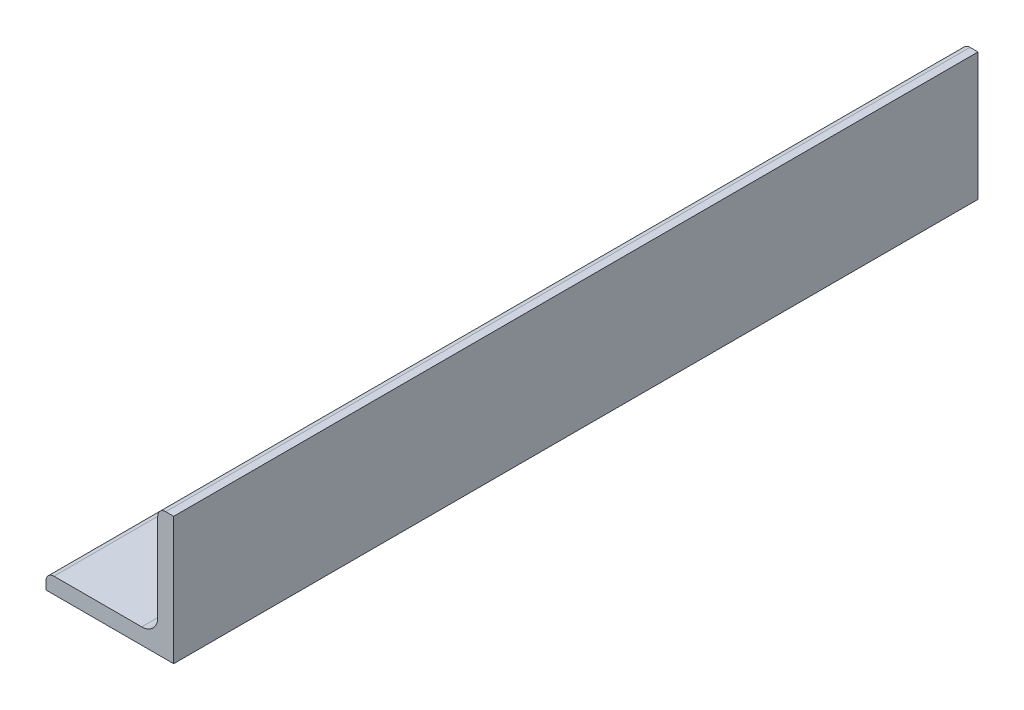
SolidWorks part; units mm, degrees
ref_plane "Front Plane" through (0, 0, 0) normal (0, 0, 1) x (1, 0, 0)
ref_plane "Top Plane" through (0, 0, 0) normal (0, 1, 0) x (1, 0, 0)
ref_plane "Right Plane" through (0, 0, 0) normal (1, 0, 0) x (0, 0, -1)
sketch "Sketch0" plane through (0, 0, 0) normal (0, 0, 1) x (1, 0, 0)
  line L0 (-12.7, -12.7) -> (12.7, -12.7)
  line L1 (12.7, -12.7) -> (12.7, 12.7)
  line L2 (12.7, 0) -> (0, 0) construction
  line L3 (0, 0) -> (0, -12.7) construction
  line L4 (9.525, -6.35) -> (9.525, 12.7) construction
  line L5 (6.35, -9.525) -> (-12.7, -9.525) construction
  arc A0 (9.525, -6.35) -> (6.35, -9.525) centre (6.35, -6.35) cw
  point P3 (8.5951, -8.5951)
  dimension "Inside Corner Radius" = 3.175
  dimension "Outside Height" = 25.4
  dimension "Inside Height" = 22.225
  dimension "Inside Width" = 22.225
  dimension "Wall Thickness" = 3.175
  dimension "D1" = 3.175
  dimension "Outside Width" = 25.4
sketch "Sketch1" plane through (0, 0, 0) normal (1, 0, 0) x (0, 0, -1)
  line L0 (609.6, 0) -> (-609.6, 0)
  point P4 (0, 0)
  dimension "Length" = 1219.2
sketch "Sketch2" plane through (0, 0, 0) normal (0, 0, 1) x (1, 0, 0)
  line L0 (-12.7, -12.7) -> (12.7, -12.7)
  line L1 (12.7, -12.7) -> (12.7, 12.7)
  line L2 (12.7, 12.7) -> (9.525, 12.7) construction
  line L3 (9.525, 11.1125) -> (9.525, -6.35)
  line L4 (6.35, -9.525) -> (-11.1125, -9.525)
  line L5 (-12.7, -12.7) -> (-12.7, -9.525) construction
  line L6 (11.1125, 12.7) -> (12.7, 12.7)
  line L7 (-12.7, -11.1125) -> (-12.7, -12.7)
  line L8 (12.7, 0) -> (0, 0) construction
  line L9 (0, 0) -> (0, -12.7) construction
  arc A0 (9.525, 11.1125) -> (11.1125, 12.7) centre (11.1125, 11.1125) cw
  arc A1 (-12.7, -11.1125) -> (-11.1125, -9.525) centre (-11.1125, -11.1125) cw
  arc A2 (9.525, -6.35) -> (6.35, -9.525) centre (6.35, -6.35) cw
  dimension "Inside Radius" = 3.175
  dimension "Height" = 25.4
  dimension "Width" = 25.4
  dimension "Thickness" = 3.175
extrude "Boss-Extrude1" add sketch "Sketch2" along normal mid plane 1219.2
sketch "Break Locations" plane through (0, 0, 0) normal (1, 0, 0) x (0, 0, -1)
  line L0 (-583.692, 0) -> (583.692, 0)
  line L1 (-609.6, -12.7) -> (-609.6, 12.7) construction
  line L2 (609.6, -12.7) -> (609.6, 12.7) construction
  point P0 (-588.01, 0)
  point P1 (588.01, 0)
  point P10 (0, 0)
  point P11 (583.692, 0)
  point P13 (-583.692, 0)
  dimension "D1" = 21.59
  dimension "D2" = 21.59
  dimension "D3" = 25.908
sketch "Sketch3" plane through (12.7, 0, 0) normal (1, 0, 0) x (0, 0, -1)
  line L0 (-609.6, -12.7) -> (609.6, -12.7) construction
  line L1 (609.6, 12.7) -> (-449.6, 12.7)
  line L2 (609.6, 12.7) -> (609.6, -12.7)
  line L3 (609.6, -12.7) -> (-449.6, -12.7)
  line L4 (-449.6, 12.7) -> (-449.6, -12.7)
  line L5 (-609.6, -12.7) -> (-609.6, 12.7) construction
  dimension "D1" = 160
extrude "Cut-Extrude2" cut sketch "Sketch3" against normal blind 30.48
equation "\"D1@Break Locations\" = .85 * \"Height@Sketch2\""
equation "\"D2@Break Locations\"=\"D1@Break Locations\""
equation "\"Thickness@Sketch2\" = \"Wall Thickness@Sketch0\""
equation "\"Height@Sketch2\" = \"Outside Height@Sketch0\""
equation "\"Width@Sketch2\" = \"Outside Width@Sketch0\""
equation "\"Inside Radius@Sketch2\" = \"Inside Corner Radius@Sketch0\""
equation "\"Length@Boss-Extrude1\" = \"Length@Sketch1\""
equation "\"D3@Break Locations\"=\"D2@Break Locations\"*1.2"
equation "\"D1@Sketch0\"=\"Wall Thickness@Sketch0\""
